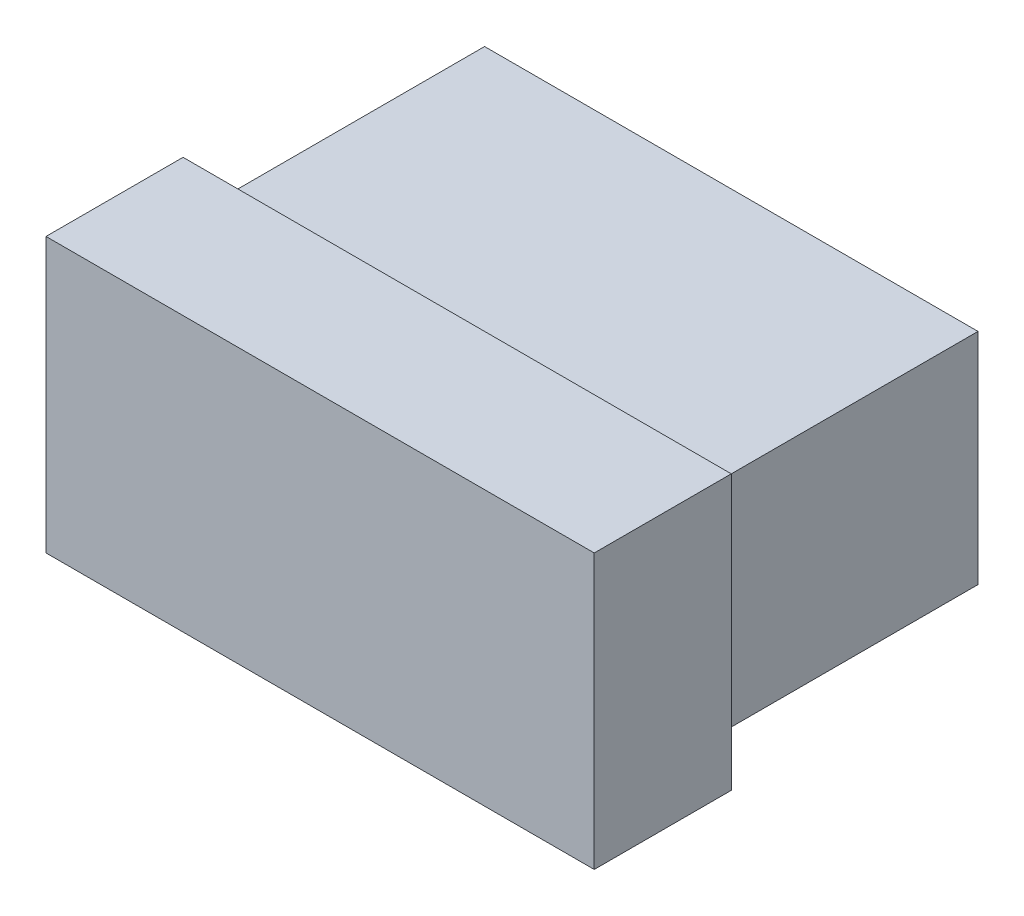
SolidWorks part; units mm, degrees
material "ABS"
ref_plane "Front Plane" through (0, 0, 0) normal (0, 0, 1) x (1, 0, 0)
ref_plane "Top Plane" through (0, 0, 0) normal (0, 1, 0) x (1, 0, 0)
ref_plane "Right Plane" through (0, 0, 0) normal (1, 0, 0) x (0, 0, -1)
sketch "Sketch1" plane through (0, 0, 0) normal (0, 0, 1) x (1, 0, 0)
  line L1 (-11.43, 5.08) -> (11.43, 5.08)
  line L2 (-11.43, 5.08) -> (-11.43, -5.08)
  line L3 (-11.43, -5.08) -> (11.43, -5.08)
  line L4 (11.43, 5.08) -> (11.43, -5.08)
  point P4 (0, 5.08)
  point P6 (11.43, 0)
  dimension "D1" = 22.86
  dimension "D2" = 10.16
extrude "Boss-Extrude1" add sketch "Sketch1" against normal blind 12.7
sketch "Sketch2" plane through (0, 0, 0) normal (0, 0, 1) x (1, 0, 0)
  line L1 (-12.7, 6.35) -> (12.7, 6.35)
  line L2 (-12.7, 6.35) -> (-12.7, -6.35)
  line L3 (-12.7, -6.35) -> (12.7, -6.35)
  line L4 (12.7, 6.35) -> (12.7, -6.35)
  point P4 (0, 6.35)
  point P6 (12.7, 0)
  dimension "D1" = 25.4
  dimension "D2" = 12.7
extrude "Boss-Extrude2" add sketch "Sketch2" along normal blind 6.35
